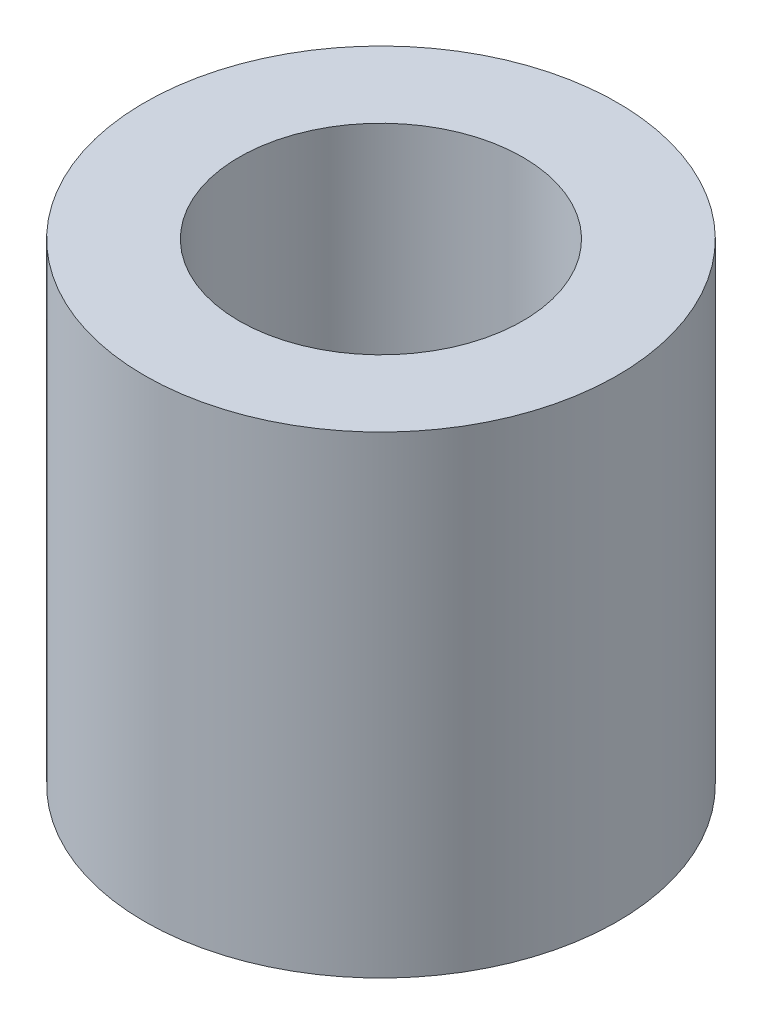
SolidWorks part; units mm, degrees
ref_plane "Front" through (0, 0, 0) normal (0, 0, 1) x (1, 0, 0)
ref_plane "Top" through (0, 0, 0) normal (0, 1, 0) x (1, 0, 0)
ref_plane "Right" through (0, 0, 0) normal (1, 0, 0) x (0, 0, -1)
sketch "Sketch1" plane through (0, 0, 0) normal (0, 1, 0) x (1, 0, 0)
  circle A0 centre (0, 0) radius 1.5
  circle A1 centre (0, 0) radius 2.5
  dimension "D1" = 3
  dimension "D2" = 5
extrude "Boss-Extrude1" add sketch "Sketch1" along normal blind 5
